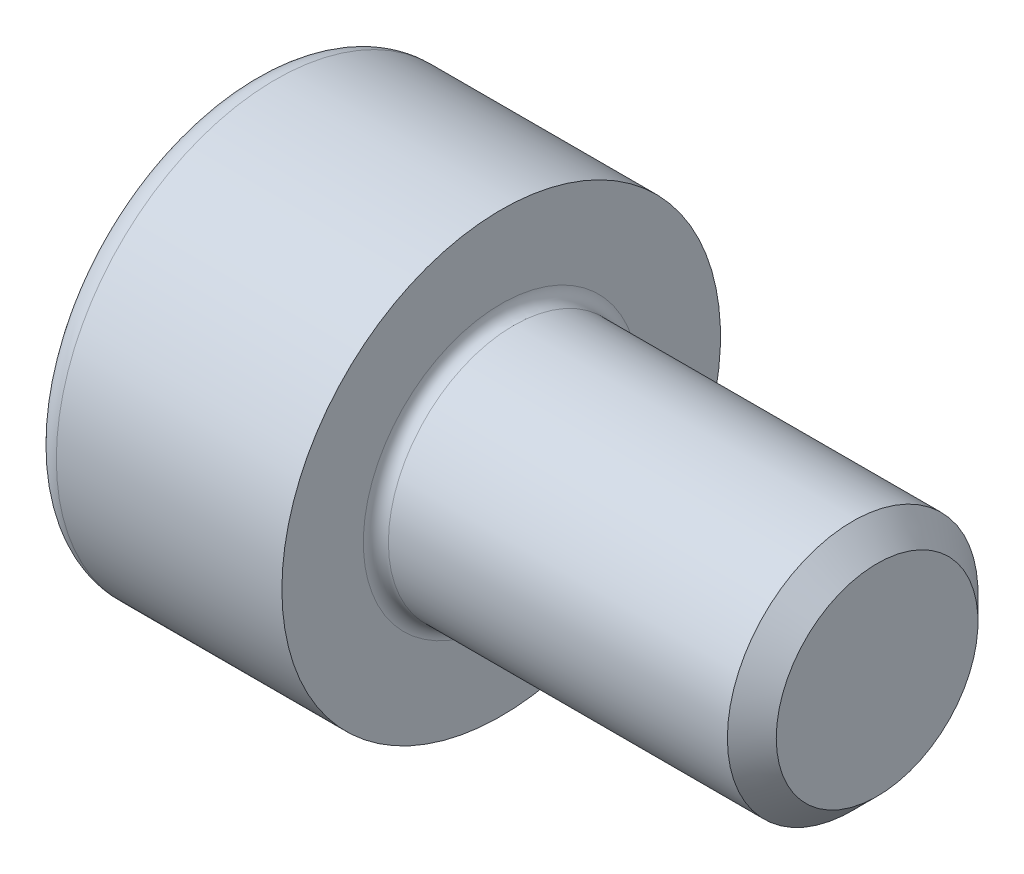
SolidWorks part; units mm, degrees
revolve "Base-Revolve" add sketch "BodySke"
sketch "BodySke" plane through (0, 0, 0) normal (0, 0, 1) x (1, 0, 0)
  line L0 (0, 0) -> (0, 3.5)
  line L1 (0, 3.5) -> (4, 3.5)
  line L2 (4, 3.5) -> (4, 2)
  line L3 (4, 2) -> (9.61, 2)
  line L4 (10, 1.61) -> (10, 0)
  line L5 (10, 0) -> (0, 0)
  line L6 (-31.75, 0) -> (127, 0) construction
  line L8 (10, 1.61) -> (9.61, 2)
  line L10 (10, -1.61) -> (9.61, -2) construction
  line L11 (4.7, 9.525) -> (4.7, 3.175) construction
  line L12 (4, 9.525) -> (4, 3.175) construction
  line L13 (-50, 9.525) -> (-50, 3.175) construction
  dimension "Head_ht" = 4
  dimension "Length" = 6
  dimension "Body_ch_ang" = 45
  dimension "Diameter" = 4
  dimension "Minor_dia" = 3.22
  dimension "Advance" = 0.7
  dimension "Thread_nom" = 6
  dimension "Thread_length" = 60
  dimension "Head_dia" = 7
cosmetic thread "ThreadCosmetic" [suppressed]
fillet "Fillet1" radius 0.2 1 edges at (4, 0, 2)
fillet "Fillet2" radius 0.4 1 edges at (0, 0, 3.5)
ref_plane "Plane1" through (0, 0, 0) normal (0, 0, 1) x (1, 0, 0)
ref_plane "Plane2" through (0, 0, 0) normal (0, 1, 0) x (1, 0, 0)
ref_plane "Plane3" through (0, 0, 0) normal (1, 0, 0) x (0, 0, -1)
sketch "Sketch2" plane through (0, 0, 0) normal (0, 0, 1) x (1, 0, 0)
  line L0 (0, 1.51) -> (2, 1.51)
  line L1 (2, 1.51) -> (2.8718, 0)
  line L2 (-31.75, 0) -> (127, 0) construction
  line L3 (2.8718, 0) -> (0, 0)
  line L4 (0, 0) -> (0, 1.51)
  line L6 (0, 0) -> (47.625, 0) construction
  dimension "D1" = 1.51
  dimension "D2" = 60
  dimension "Depth" = 2
revolve "Hex-PreBroach" cut sketch "Sketch2" angle 360 about L6
sketch "Sketch3" plane through (0, 0, 0) normal (-1, 0, 0) x (0, 0.5, 0.866)
  line L0 (0.8718, 1.51) -> (-0.8718, 1.51)
  line L1 (-0.8718, 1.51) -> (-1.7436, 0)
  line L2 (0.8718, 1.51) -> (1.7436, 0)
  line L3 (0.8718, -1.51) -> (1.7436, 0)
  line L4 (0.8718, -1.51) -> (-0.8718, -1.51)
  line L5 (-0.8718, -1.51) -> (-1.7436, 0)
  dimension "D1" = 1.51
  dimension "D2" = 1.51
  dimension "Hex_size" = 3.02
extrude "Hex" cut sketch "Sketch3" against normal blind 2
sketch "ThdSchSke" plane through (0, 0, 0) normal (0, 0, 1) x (1, 0, 0)
  line L0 (6.1, -1.61) -> (5.8269, -2)
  line L1 (6.1, -1.61) -> (6.3731, -2)
  line L2 (6.3731, -2) -> (6.3731, -2.5)
  line L3 (-3.175, 0) -> (5.1513, 0) construction
  line L4 (0, 3.1) -> (0, -3.1) construction
  line L5 (6.3731, -2.5) -> (5.8269, -2.5)
  line L6 (5.8269, -2.5) -> (5.8269, -2)
  dimension "Thread_minor" = 3.22
  dimension "Diameter" = 4
  dimension "Start" = 6.1
revolve "ThreadSchematic" [suppressed] cut sketch "ThdSchSke" angle 360 about L3
pattern_linear "ThdSchPat" [suppressed]
equation "\"D2@Sketch3\" = \"Hex_size@Sketch3\" / 2"
equation "\"D1@Sketch3\" = \"Hex_size@Sketch3\" / 2"
equation "\"D1@Sketch2\" = \"Hex_size@Sketch3\" / 2"
equation "\"Thread_minor@ThreadCosmetic\"  =  \"Minor_dia@BodySke\""
equation "\"Depth@Sketch2\" =  \"Key_eng@Hex\""
equation "\"Thread_length@ThreadCosmetic\" = ((sgn( (\"Length@BodySke\" - \"Advance@BodySke\" * 3.0) - \"Thread_nom@BodySke\" )-1)*( (\"Length@BodySke\" - \"Advance@BodySke\" * 3.0) - \"Thread_nom@BodySke\" ))/-2+ \"Thread_nom@BodySke\""
equation "\"Thread_minor@ThdSchSke\" = \"Minor_dia@BodySke\""
equation "\"Diameter@ThdSchSke\" = \"Diameter@BodySke\""
equation "\"Overcut@ThdSchSke\" = \"Diameter@BodySke\" * 1.25"
equation "\"Start@ThdSchSke\" = \"Head_ht@BodySke\" + \"Length@BodySke\" - \"Thread_length@ThreadCosmetic\"  '---Non-countersunk---"
equation "\"Num_threads@ThdSchPat\" = int( \"Thread_length@ThreadCosmetic\" / \"Advance@BodySke\" + 0.999 )  + 1"
equation "\"Advance@ThdSchPat\" = \"Thread_length@ThreadCosmetic\" /  (\"Num_threads@ThdSchPat\" - 1) 'relax it"
equation "\"Num_threads@ThdSchPat\" = \"Num_threads@ThdSchPat\" - sgn( \"Num_threads@ThdSchPat\" - 1) '---chamfered tips only---"
